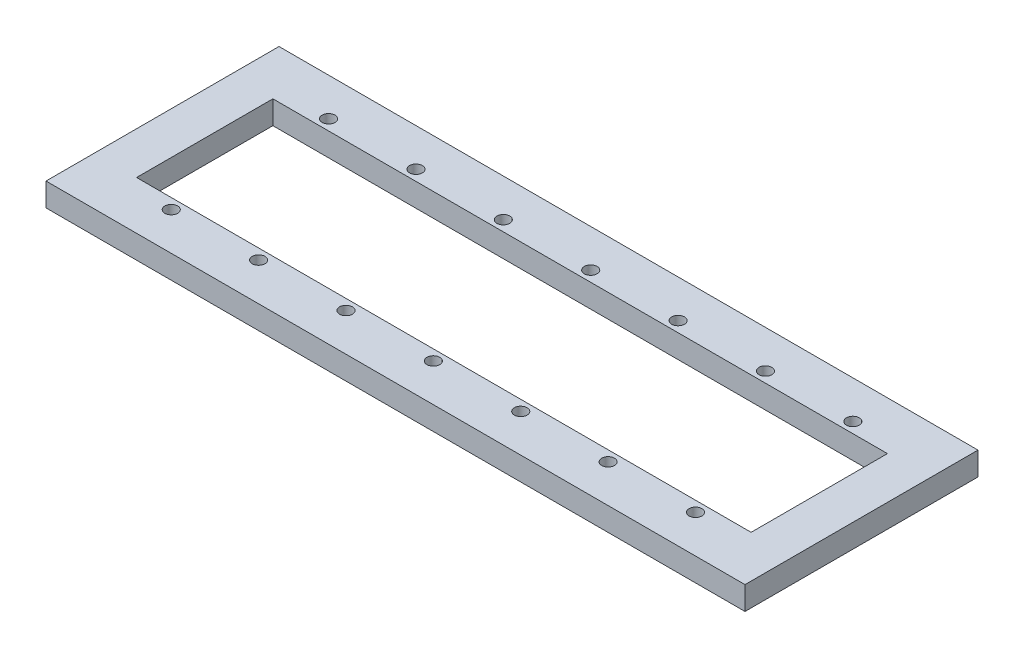
SolidWorks part; units mm, degrees
ref_plane "Front Plane" through (0, 0, 0) normal (0, 0, 1) x (1, 0, 0)
ref_plane "Top Plane" through (0, 0, 0) normal (0, 1, 0) x (1, 0, 0)
ref_plane "Right Plane" through (0, 0, 0) normal (1, 0, 0) x (0, 0, -1)
sketch "Sketch1" plane through (0, 0, 0) normal (0, 1, 0) x (1, 0, 0)
  line L1 (60, 20) -> (-60, 20)
  line L2 (60, 20) -> (60, -20)
  line L3 (60, -20) -> (-60, -20)
  line L4 (-60, 20) -> (-60, -20)
  line L5 (60, 20) -> (-60, -20) construction
  line L6 (60, -20) -> (-60, 20) construction
  point P0 (0, 0)
  dimension "D1" = 40
  dimension "D2" = 120
extrude "Boss-Extrude1" add sketch "Sketch1" along normal blind 4
sketch "Sketch2" plane through (0, 4, 0) normal (0, 1, 0) x (1, 0, 0)
  line L0 (-60, 0) -> (60, 0) construction
  line L1 (-60, 20) -> (-60, -20) construction
  line L2 (60, -20) -> (60, 20) construction
  line L3 (-36.2486, 11.5) -> (-36.2486, -11.5)
  line L4 (-38.7486, 11.5) -> (-51.2486, 11.5)
  line L5 (-38.7486, 11.5) -> (-38.7486, -11.5)
  line L6 (-38.7486, -11.5) -> (-51.2486, -11.5)
  line L7 (-51.2486, 11.5) -> (-51.2486, -11.5)
  line L8 (-38.7486, 11.5) -> (-51.2486, -11.5) construction
  line L9 (-38.7486, -11.5) -> (-51.2486, 11.5) construction
  line L10 (-23.7486, 11.5) -> (-36.2486, 11.5)
  line L11 (-23.7486, 11.5) -> (-23.7486, -11.5)
  line L12 (-23.7486, -11.5) -> (-36.2486, -11.5)
  line L13 (-21.2486, 11.5) -> (-21.2486, -11.5)
  line L14 (-8.7486, 11.5) -> (-21.2486, 11.5)
  line L15 (-8.7486, 11.5) -> (-8.7486, -11.5)
  line L16 (-8.7486, -11.5) -> (-21.2486, -11.5)
  line L17 (-6.2486, 11.5) -> (-6.2486, -11.5)
  line L18 (6.2514, 11.5) -> (-6.2486, 11.5)
  line L19 (6.2514, 11.5) -> (6.2514, -11.5)
  line L20 (6.2514, -11.5) -> (-6.2486, -11.5)
  line L21 (8.7514, 11.5) -> (8.7514, -11.5)
  line L22 (21.2514, 11.5) -> (8.7514, 11.5)
  line L23 (21.2514, 11.5) -> (21.2514, -11.5)
  line L24 (21.2514, -11.5) -> (8.7514, -11.5)
  line L25 (23.7514, 11.5) -> (23.7514, -11.5)
  line L26 (36.2514, 11.5) -> (23.7514, 11.5)
  line L27 (36.2514, 11.5) -> (36.2514, -11.5)
  line L28 (36.2514, -11.5) -> (23.7514, -11.5)
  line L29 (38.7514, 11.5) -> (38.7514, -11.5)
  line L30 (51.2514, 11.5) -> (38.7514, 11.5)
  line L31 (51.2514, 11.5) -> (51.2514, -11.5)
  line L32 (51.2514, -11.5) -> (38.7514, -11.5)
  circle A0 centre (-44.9986, 13.5107) radius 1.1
  circle A1 centre (-44.9986, -13.5) radius 1.1
  circle A2 centre (-29.9986, 13.5107) radius 1.1
  circle A3 centre (-29.9986, -13.5) radius 1.1
  circle A4 centre (-14.9986, 13.5107) radius 1.1
  circle A5 centre (-14.9986, -13.5) radius 1.1
  circle A6 centre (0.0014, 13.5107) radius 1.1
  circle A7 centre (0.0014, -13.5) radius 1.1
  circle A8 centre (15.0014, 13.5107) radius 1.1
  circle A9 centre (15.0014, -13.5) radius 1.1
  circle A10 centre (30.0014, 13.5107) radius 1.1
  circle A11 centre (30.0014, -13.5) radius 1.1
  circle A12 centre (45.0014, 13.5107) radius 1.1
  circle A13 centre (45.0014, -13.5) radius 1.1
  point P6 (-44.9986, 0)
  dimension "D8" = 2.2
  dimension "D9" = 2.2
  dimension "D1" = 12.5
  dimension "D2" = 23
  dimension "D4" = 2.5
  dimension "D5" = 2.5
  dimension "D6" = 8.7514
  dimension "D7" = 8.7486
  dimension "D10" = 2.0107
  dimension "D11" = 2
  dimension "D3" = 7
  dimension "D12" = 7
extrude "Cut-Extrude1" cut sketch "Sketch2" against normal through all
sketch "Sketch3" plane through (0, 4, 0) normal (0, 1, 0) x (1, 0, 0)
  line L0 (-38.7486, 11.5) -> (-51.2486, 11.5) construction
  line L1 (-52.7486, 11.7) -> (52.7514, 11.7)
  line L2 (-52.7486, 11.7) -> (-52.7486, -11.7)
  line L3 (-52.7486, -11.7) -> (52.7514, -11.7)
  line L4 (52.7514, 11.7) -> (52.7514, -11.7)
  line L5 (-51.2486, 11.5) -> (-51.2486, -11.5) construction
  line L6 (51.2514, -11.5) -> (51.2514, 11.5) construction
  line L7 (-51.2486, -11.5) -> (-38.7486, -11.5) construction
  dimension "D1" = 0.2
  dimension "D2" = 1.5
  dimension "D3" = 1.5
  dimension "D4" = 0.2
  dimension "D5" = 0.2
extrude "Cut-Extrude2" cut sketch "Sketch3" against normal through all
